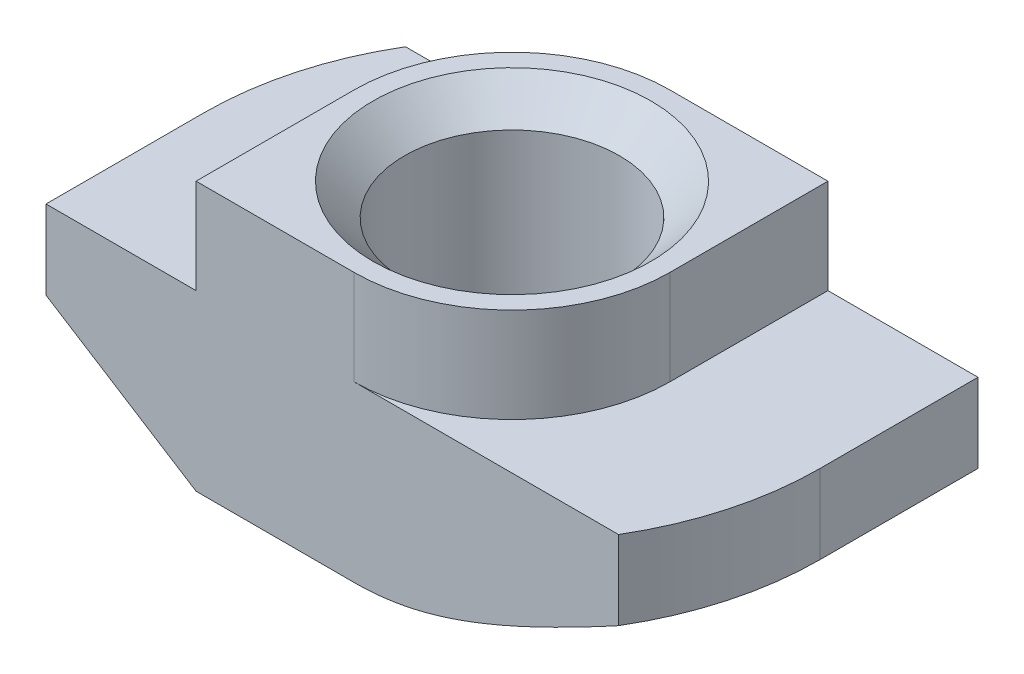
SolidWorks part; units mm, degrees
material "Сталь 20  ГОСТ 1050-2013"
ref_plane "Спереди" through (0, 0, 0) normal (0, 0, 1) x (1, 0, 0)
ref_plane "Сверху" through (0, 0, 0) normal (0, 1, 0) x (1, 0, 0)
ref_plane "Справа" through (0, 0, 0) normal (1, 0, 0) x (0, 0, -1)
sketch "Эскиз1" plane through (0, 0, 0) normal (0, 0, 1) x (1, 0, 0)
  line L0 (5, 0) -> (-5, 0)
  line L1 (-5, 0) -> (-5, -3)
  line L2 (-5, -3) -> (-9.75, -3)
  line L3 (-9.75, -3) -> (-9.75, -8.5)
  line L4 (-9.75, -8.5) -> (9.75, -8.5)
  line L5 (0, -8.5) -> (0, 0) construction
  line L6 (9.75, -3) -> (9.75, -8.5)
  line L7 (5, -3) -> (9.75, -3)
  line L8 (5, 0) -> (5, -3)
  dimension "D1" = 10
  dimension "D2" = 19.5
  dimension "D3" = 8.5
  dimension "D4" = 3
extrude "Бобышка-Вытянуть1" add sketch "Эскиз1" along normal mid plane 10
hole_wizard "Отверстие обработанное метчиком M81" positions "Эскиз2" profile "Эскиз3" tap size "M8" standard "ISO" end condition up to next
sketch "Эскиз2" plane through (0, 0, 0) normal (0, 1, 0) x (1, 0, 0)
  point P0 (0, 0)
sketch "Эскиз3" plane through (0, 0, 0) normal (1, 0, 0) x (0, 0, 1)
  line L0 (0, 0) -> (0, 8.5)
  line L1 (0, 8.5) -> (4.4, 8.5)
  line L2 (3.4, 7.5) -> (3.4, 1)
  line L3 (3.4, 1) -> (4.4, 0)
  line L5 (4.4, 0) -> (0, 0)
  line L6 (-3.4, 1) -> (-4.4, 0) construction
  line L7 (4.4, 8.5) -> (3.4, 7.5)
  line L8 (-4.4, 8.5) -> (-3.4, 7.5) construction
  line L11 (0, -6.35) -> (0, 107.95) construction
  dimension "Диаметр проходного сверла" = 6.8
  dimension "Глубина проходного сверла" = 8.5
  dimension "Диаметр передней зенковки" = 8.8
  dimension "Угол передней зенковки" = 90
  dimension "Диаметр задней зенковки" = 8.8
  dimension "Угол задней зенковки" = 90
cosmetic thread "Отверстие резьбы1" parameters "D2"=8
sketch "Эскиз4" plane through (0, 0, 0) normal (0, 1, 0) x (1, 0, 0)
  line L0 (-5, 5) -> (-5, 0)
  line L1 (-5, -5) -> (-5, 5) construction
  line L2 (5, 5) -> (-5, 5) construction
  line L3 (0, 5) -> (-5, 5)
  line L4 (0, -5) -> (5, -5)
  line L5 (5, -5) -> (-5, -5) construction
  line L6 (5, -5) -> (5, 0)
  line L7 (5, -5) -> (5, 5) construction
  arc A0 (-5, 0) -> (0, 5) centre (0, 0) cw
  arc A1 (5, 0) -> (0, -5) centre (0, 0) cw
extrude "Вырез-Вытянуть1" cut sketch "Эскиз4" against normal up to surface (3 mm away) up to face at (-7.375, -3, 0)
sketch "Эскиз5" plane through (0, -3, 0) normal (0, 1, 0) x (1, 0, 0)
  line L0 (-9.75, 0) -> (-9.75, 5)
  line L1 (-9.75, -5) -> (-9.75, 5) construction
  line L2 (-9.75, 5) -> (-8.3703, 5)
  line L3 (0, 5) -> (-9.75, 5) construction
  line L4 (9.75, 0) -> (9.75, -5)
  line L5 (9.75, -5) -> (9.75, 5) construction
  line L6 (9.75, -5) -> (8.3703, -5)
  line L7 (9.75, -5) -> (0, -5) construction
  arc A0 (-8.3703, 5) -> (-9.75, 0) centre (0, 0) ccw
  arc A2 (9.75, 0) -> (8.3703, -5) centre (0, 0) cw
  point P19 (0, 0)
extrude "Вырез-Вытянуть2" cut sketch "Эскиз5" against normal through all
sketch "Эскиз6" plane through (0, 0, 5) normal (0, 0, 1) x (1, 0, 0)
  line L0 (-9.75, -5.5) -> (-9.75, -8.5)
  line L1 (-9.75, -3) -> (-9.75, -8.5) construction
  line L2 (-9.75, -8.5) -> (-5, -8.5)
  line L3 (-9.75, -8.5) -> (8.3703, -8.5) construction
  line L4 (-5, -8.5) -> (-9.75, -5.5)
  line L5 (-5, -3) -> (-9.75, -3) construction
  line L6 (-5, 0) -> (-5, -3) construction
  point P10 (0, 0)
  dimension "D1" = 2.5
sketch "Эскиз7" plane through (0, -8.5, 0) normal (0, -1, 0) x (1, 0, 0)
  line L0 (0, 9.75) -> (-9.75, 9.75)
  line L1 (-9.75, 9.75) -> (-9.75, 0)
  line L2 (0, -9.75) -> (9.75, -9.75)
  line L3 (9.75, -9.75) -> (9.75, 0)
  arc A0 (-9.75, 0) -> (0, -9.75) centre (0, 0) ccw
  arc A1 (9.75, 0) -> (0, 9.75) centre (0, 0) ccw
sweep "Вырез-По траектории1" cut profiles "Эскиз6" path "Эскиз7"
